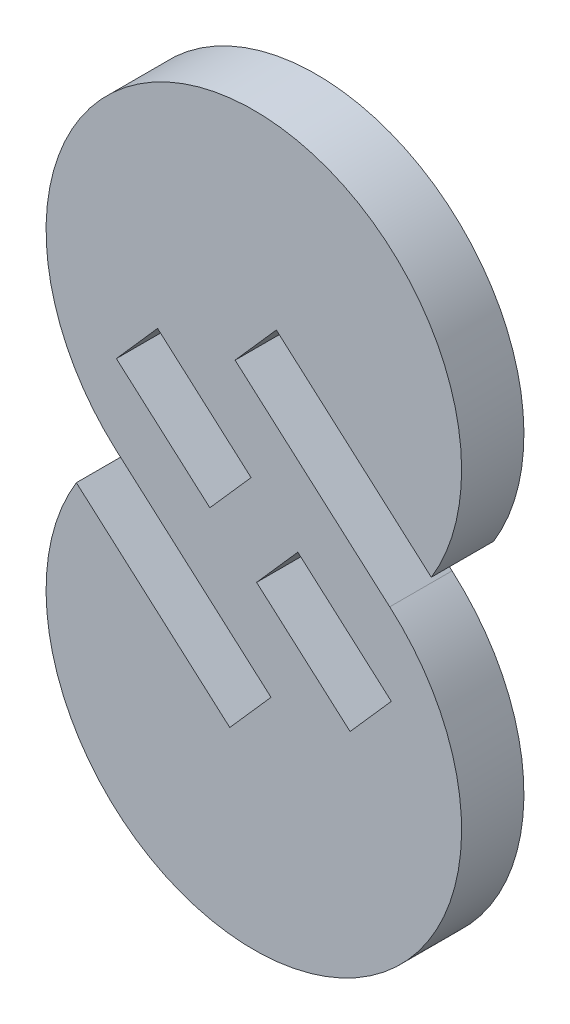
SolidWorks part; units mm, degrees
ref_plane "Alzado" through (0, 0, 0) normal (0, 0, 1) x (1, 0, 0)
ref_plane "Planta" through (0, 0, 0) normal (0, 1, 0) x (1, 0, 0)
ref_plane "Vista lateral" through (0, 0, 0) normal (1, 0, 0) x (0, 0, -1)
sketch "Croquis1" plane through (0, 0, 0) normal (0, 0, 1) x (1, 0, 0)
  line L0 (0, 0) -> (0, -15)
  line L1 (0, -15) -> (0, -14.0625)
  line L5 (-6.6144, -7.5) -> (0.8268, -14.0626)
  line L7 (0.8268, -14.0626) -> (-1.1576, -16.3125)
  line L8 (-8.5419, -9.8001) -> (-1.1576, -16.3125)
  line L9 (1.0832, 1.3777) -> (8.5416, -5.2001)
  line L11 (-0.9011, -0.8723) -> (6.5401, -7.4349)
  line L12 (1.0832, 1.3777) -> (-0.9011, -0.8723)
  line L14 (0.8268, -14.0626) -> (9.9562, -14.0626) construction
  line L16 (0.8268, -14.0626) -> (-1.1576, -16.3125)
  line L17 (0.8268, -14.0626) -> (-6.6144, -7.5)
  line L18 (-1.1576, -16.3125) -> (-8.5419, -9.8001)
  line L20 (-0.9011, -0.8723) -> (1.0832, 1.3777)
  line L21 (-0.9011, -0.8723) -> (6.5401, -7.4349)
  line L22 (1.0832, 1.3777) -> (8.5416, -5.2001)
  arc A0 (8.5416, -5.2001) -> (-6.6144, -7.5) centre (0, 0) ccw
  arc A1 (-8.5419, -9.8001) -> (6.5401, -7.4349) centre (0, -15) ccw
  point P24 (0, 0)
  point P27 (0, -15)
extrude "Saliente-Extruir1" add sketch "Croquis1" along normal blind 3 contours L9 A0 L5 L7 L8 A1 L11 L12
sketch "Croquis2" plane through (0, 0, 0) normal (0, 0, -1) x (-1, 0, 0)
  line L0 (-8.5416, -5.2001) -> (8.5416, -9.8003)
  line L1 (8.5419, -9.8001) -> (1.1576, -16.3125) construction
  line L2 (0, -7.5002) -> (0, 3.8843)
  line L3 (0.9011, -0.8723) -> (6.6882, -7.4342)
  line L4 (-4.6328, -13.586) -> (-0.1328, -9.6174)
  line L5 (-4.6328, -13.586) -> (-6.6171, -11.336)
  line L6 (-6.6171, -11.336) -> (-2.1172, -7.3674)
  line L7 (6.6171, -3.6644) -> (4.6328, -1.4144)
  line L8 (-4.6328, -13.586) -> (4.6328, -1.4144) construction
  line L9 (-6.6171, -11.336) -> (6.6171, -3.6644) construction
  line L10 (-1.0832, 1.3777) -> (0.9011, -0.8723) construction
  line L11 (0.9011, -0.8723) -> (-6.5401, -7.4349) construction
  line L12 (0.1328, -5.383) -> (2.1172, -7.633)
  line L13 (-2.1172, -7.3674) -> (-0.1328, -9.6174)
  line L14 (0.1328, -5.383) -> (4.6328, -1.4144)
  line L15 (2.1172, -7.633) -> (6.6171, -3.6644)
  arc A1 (6.6144, -7.5) -> (-8.5416, -5.2001) centre (0, 0) ccw construction
  point P16 (5.625, -2.5394)
extrude "Cortar-Extruir2" cut sketch "Croquis2" against normal up to next contours L6 L12 L4 L3 | L4 L7 L6 L3 | L13 L6 L5 L4
equation "\"Diameter of shape\"= 20mm"
equation "\"Inclination of left cut\"= 138.59°"
equation "\"Distance between circles center\"= 15mm"
equation "\"Inclination of right cut\"= 41.41°"
equation "\"Material thickness\"= 3mm"
equation "\"Distance S cut in X\"= 17.0835589mm"
equation "\"Distance S cut in Y\"= 4.60"
equation "\"D1@Croquis1\"=\"Diameter of shape\""
equation "\"D2@Croquis1\"=\"Distance between circles center\""
equation "\"D3@Croquis1\"=\"Material thickness\""
equation "\"D5@Croquis1\"=\"Material thickness\""
equation "\"D10@Croquis1\"=\"Inclination of right cut\""
equation "\"D8@Croquis1\"=\"Inclination of left cut\""
equation "\"D6@Croquis1\"=\"Distance S cut in Y\""
equation "\"D9@Croquis1\"=\"Distance S cut in X\""
equation "\"D1@Croquis2\"=\"Material thickness\""
equation "\"D2@Croquis2\"=\"Material thickness\"*2"
equation "\"D3@Croquis2\"=\"Material thickness\""
